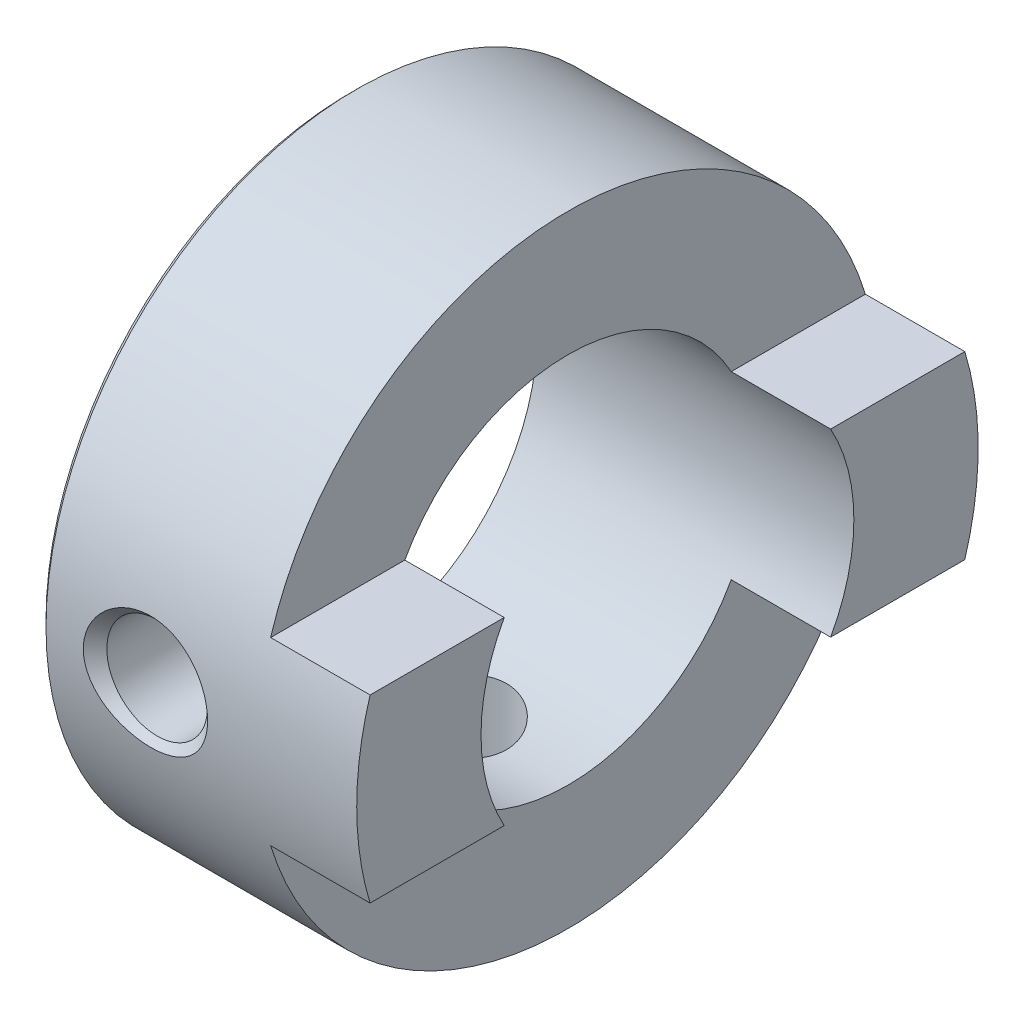
SolidWorks part; units mm, degrees
ref_plane "Front Plane" through (0, 0, 0) normal (0, 0, 1) x (1, 0, 0)
ref_plane "Top Plane" through (0, 0, 0) normal (0, 1, 0) x (1, 0, 0)
ref_plane "Right Plane" through (0, 0, 0) normal (1, 0, 0) x (0, 0, -1)
ref_plane "Plane1" through (0, 0, 0) normal (0, 0, 1) x (1, 0, 0)
sketch "Sketch1" plane through (0, 0, 0) normal (0, 0, 1) x (1, 0, 0)
  line L0 (0, 9.8) -> (0, 6)
  line L1 (0, 6) -> (10.2, 6)
  line L2 (10.2, 6) -> (10.2, 10)
  line L3 (10.2, 10) -> (0.2, 10)
  line L4 (0.2, 10) -> (0, 9.8)
  line L5 (10.2, 0) -> (0, 0) construction
revolve "Revolve1" add sketch "Sketch1" angle 360 about L5
ref_plane "Plane2" through (10.2, 0, 0) normal (1, 0, 0) x (0, 0, -1)
sketch "Sketch2" plane through (10.2, 0, 0) normal (1, 0, 0) x (0, 0, -1)
  line L0 (-11, 10.5) -> (-11, -10.5)
  line L1 (-11, -10.5) -> (11, -10.5)
  line L2 (11, -10.5) -> (11, 10.5)
  line L3 (11, 10.5) -> (-11, 10.5)
  line L4 (-10, 2.9) -> (-10, -2.9)
  line L5 (-10, -2.9) -> (10, -2.9)
  line L6 (10, -2.9) -> (10, 2.9)
  line L7 (10, 2.9) -> (-10, 2.9)
extrude "Cut-Extrude1" cut sketch "Sketch2" against normal blind 3.2
ref_plane "Plane3" through (3.4, 0, 0) normal (1, 0, 0) x (0, 0, -1)
sketch "Sketch3" plane through (3.4, 0, 0) normal (1, 0, 0) x (0, 0, -1)
  line L0 (-10, 0) -> (-10, 2)
  line L1 (-10, 2) -> (-9.621, 1.621)
  line L2 (-9.621, 1.621) -> (0, 1.621)
  line L3 (0, 1.621) -> (0, 0)
  line L4 (0, 0) -> (-10, 0)
  line L5 (0, 0) -> (-10, 0) construction
revolve "Cut-Revolve1" cut sketch "Sketch3" angle 360 about L5
ref_plane "Plane4" through (3.4, 0, 0) normal (1, 0, 0) x (0, 0, -1)
sketch "Sketch4" plane through (3.4, 0, 0) normal (1, 0, 0) x (0, 0, -1)
  line L0 (0, -10) -> (-2, -10)
  line L1 (-2, -10) -> (-1.621, -9.621)
  line L2 (-1.621, -9.621) -> (-1.621, 0)
  line L3 (-1.621, 0) -> (0, 0)
  line L4 (0, 0) -> (0, -10)
  line L5 (0, 0) -> (0, -10) construction
revolve "Cut-Revolve2" cut sketch "Sketch4" angle 360 about L5
